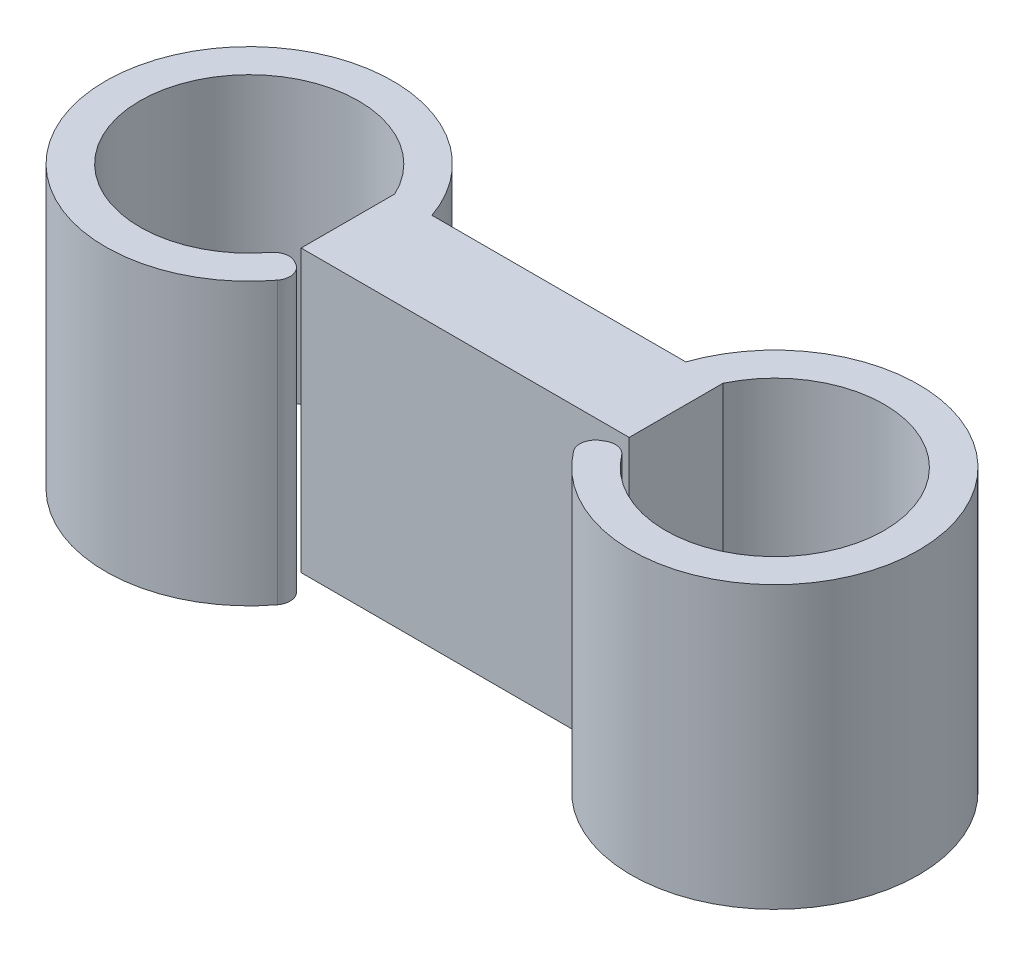
SolidWorks part; units mm, degrees
ref_plane "Front Plane" through (0, 0, 0) normal (0, 0, 1) x (1, 0, 0)
ref_plane "Top Plane" through (0, 0, 0) normal (0, 1, 0) x (1, 0, 0)
ref_plane "Right Plane" through (0, 0, 0) normal (1, 0, 0) x (0, 0, -1)
sketch "Sketch1" plane through (0, 0, 0) normal (0, 1, 0) x (1, 0, 0)
  line L1 (-10.5, 3) -> (10.5, 3)
  line L2 (-10.5, 3) -> (-10.5, -3)
  line L3 (-10.5, -3) -> (10.5, -3)
  line L4 (10.5, 3) -> (10.5, -3)
  line L5 (-10.5, 3) -> (10.5, -3) construction
  line L6 (-10.5, -3) -> (10.5, 3) construction
  point P4 (0, 0)
  point P5 (0, 0)
  dimension "D1" = 6
  dimension "D2" = 21
extrude "Boss-Extrude1" add sketch "Sketch1" along normal blind 18
sketch "Sketch2" plane through (0, 18, 0) normal (0, 1, 0) x (1, 0, 0)
  line L0 (-16.8246, 0) -> (0, 0) construction
  line L1 (0, 0) -> (0, 3) construction
  line L2 (10.5, 3) -> (-10.5, 3) construction
  line L3 (-10.5, 3) -> (-8.1274, 3)
  line L4 (-10.7624, -3.5) -> (-8.8571, -4.6)
  line L5 (-16.8246, 0) -> (-10.7624, -3.5) construction
  line L6 (16.8246, 0) -> (10.7624, -3.5) construction
  line L7 (10.7624, -3.5) -> (8.8571, -4.6)
  line L8 (10.5, 3) -> (8.1274, 3)
  arc A0 (-10.5, 3) -> (-10.7624, -3.5) centre (-16.8246, 0) ccw
  arc A2 (-8.1274, 3) -> (-8.8571, -4.6) centre (-16.8246, 0) ccw
  arc A4 (-8.8571, -4.6) -> (-7.6246, 0) centre (-16.8246, 0) ccw construction
  arc A5 (-10.7624, -3.5) -> (-9.8246, 0) centre (-16.8246, 0) ccw construction
  arc A6 (-9.8246, 0) -> (-10.5, 3) centre (-16.8246, 0) ccw construction
  arc A7 (-7.6246, 0) -> (-8.1274, 3) centre (-16.8246, 0) ccw construction
  arc A8 (7.6246, 0) -> (8.1274, 3) centre (16.8246, 0) cw construction
  arc A9 (9.8246, 0) -> (10.5, 3) centre (16.8246, 0) cw construction
  arc A10 (10.7624, -3.5) -> (9.8246, 0) centre (16.8246, 0) cw construction
  arc A11 (8.8571, -4.6) -> (7.6246, 0) centre (16.8246, 0) cw construction
  arc A12 (8.1274, 3) -> (8.8571, -4.6) centre (16.8246, 0) cw
  arc A13 (10.5, 3) -> (10.7624, -3.5) centre (16.8246, 0) cw
  dimension "D1" = 14
  dimension "D2" = 2.2
  dimension "D3" = 30
extrude "Boss-Extrude2" add sketch "Sketch2" against normal up to surface (18 mm away) up to face at (0, 0, 0)
fillet "Fillet1" radius 1 4 edges at (10.7624, 9, 3.5) (8.8571, 9, 4.6) (-8.8571, 9, 4.6) (-10.7624, 9, 3.5)
